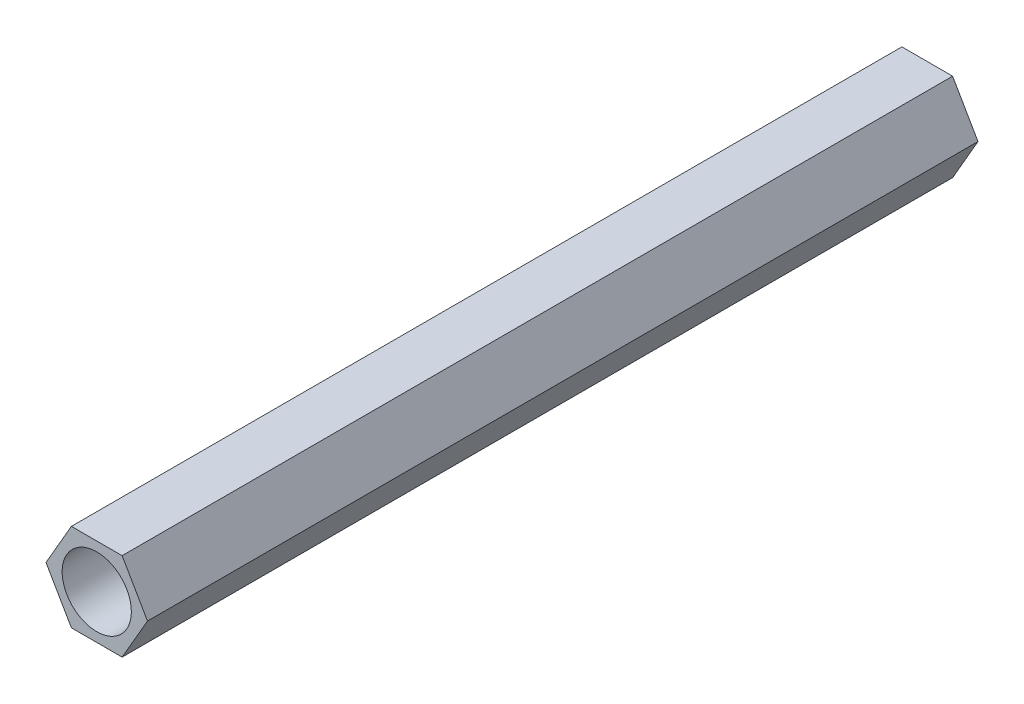
SolidWorks part; units mm, degrees
material "3003 Alloy"
ref_plane "Front Plane" through (0, 0, 0) normal (0, 0, 1) x (1, 0, 0)
ref_plane "Top Plane" through (0, 0, 0) normal (0, 1, 0) x (1, 0, 0)
ref_plane "Right Plane" through (0, 0, 0) normal (1, 0, 0) x (0, 0, -1)
sketch "Sketch1" plane through (0, 0, 0) normal (0, 0, 1) x (1, 0, 0)
  line L1 (3.6662, 0) -> (1.8331, 3.175)
  line L2 (1.8331, 3.175) -> (-1.8331, 3.175)
  line L3 (-1.8331, 3.175) -> (-3.6662, 0)
  line L4 (-3.6662, 0) -> (-1.8331, -3.175)
  line L5 (-1.8331, -3.175) -> (1.8331, -3.175)
  line L6 (1.8331, -3.175) -> (3.6662, 0)
  circle A0 centre (0, 0) radius 3.6662 construction
  circle A1 centre (0, 0) radius 2.5
  dimension "D2" = 5
  dimension "D1" = 6.35
extrude "Boss-Extrude1" add sketch "Sketch1" along normal blind 60
